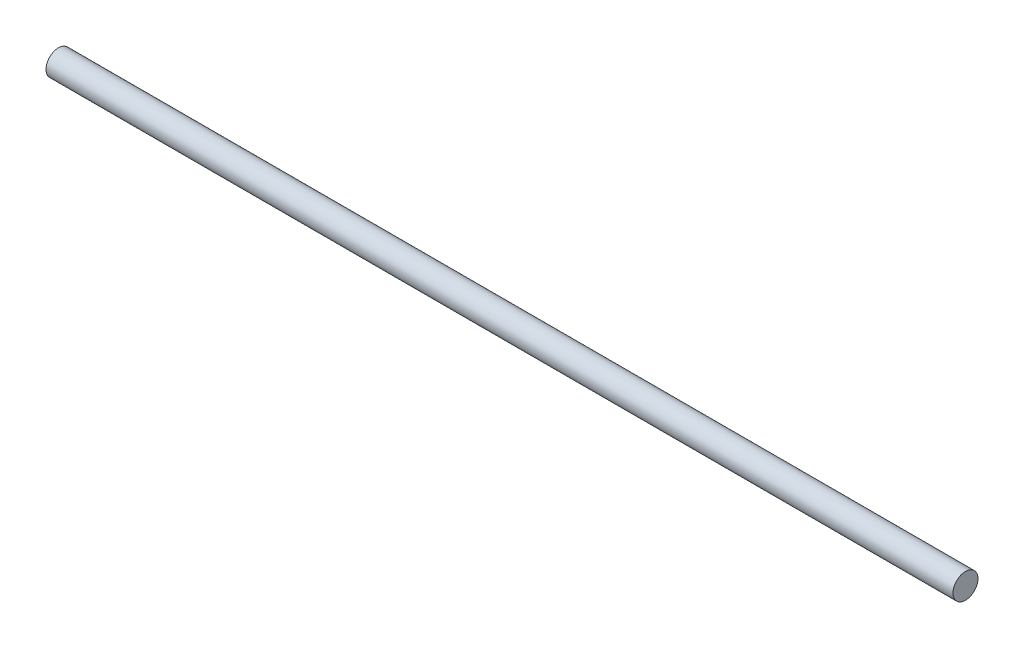
SolidWorks part; units mm, degrees
ref_plane "Front Plane" through (0, 0, 0) normal (0, 0, 1) x (1, 0, 0)
ref_plane "Top Plane" through (0, 0, 0) normal (0, 1, 0) x (1, 0, 0)
ref_plane "Right Plane" through (0, 0, 0) normal (1, 0, 0) x (0, 0, -1)
sketch "Sketch1" plane through (0, 0, 0) normal (1, 0, 0) x (0, 0, -1)
  circle A0 centre (0, 0) radius 4
  dimension "D1" = 8
extrude "Boss-Extrude1" add sketch "Sketch1" along normal blind 290
